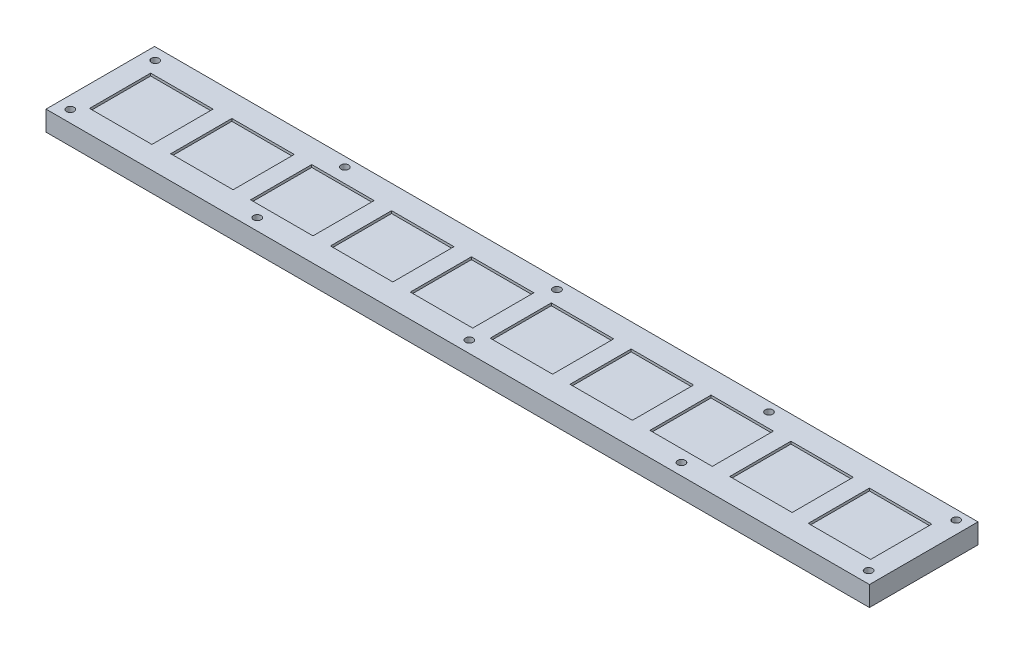
SolidWorks part; units mm, degrees
ref_plane "Front Plane" through (0, 0, 0) normal (0, 0, 1) x (1, 0, 0)
ref_plane "Top Plane" through (0, 0, 0) normal (0, 1, 0) x (1, 0, 0)
ref_plane "Right Plane" through (0, 0, 0) normal (1, 0, 0) x (0, 0, -1)
sketch "Sketch1" plane through (0, 0, 0) normal (0, 1, 0) x (1, 0, 0)
  line L1 (0, 0) -> (-330, 0)
  line L2 (0, 0) -> (0, 43.5)
  line L3 (0, 43.5) -> (-330, 43.5)
  line L4 (-330, 0) -> (-330, 43.5)
  dimension "D1" = 330
  dimension "D2" = 43.5
extrude "Boss-Extrude1" add sketch "Sketch1" along normal blind 8
sketch "Sketch6" plane through (0, 8, 0) normal (0, 1, 0) x (1, 0, 0)
  line L0 (-330, 21.75) -> (0, 21.75) construction
  line L1 (-330, 43.5) -> (-330, 0) construction
  line L2 (0, 0) -> (0, 43.5) construction
  line L3 (0, 21.75) -> (-165, 21.75) construction
  line L4 (-165, 21.75) -> (-165, 91.0768) construction
  line L5 (-165, 91.0768) -> (-165, -46.8957) construction
  line L6 (-225.5094, 9.5) -> (-225.5094, 34)
  line L7 (-193.5047, 9.5) -> (-168.5, 9.5)
  line L8 (-193.5047, 9.5) -> (-193.5047, 34)
  line L9 (-193.5047, 34) -> (-168.5, 34)
  line L10 (-168.5, 9.5) -> (-168.5, 34)
  line L11 (-193.5047, 9.5) -> (-168.5, 34) construction
  line L12 (-193.5047, 34) -> (-168.5, 9.5) construction
  line L13 (-225.5094, 34) -> (-200.5047, 34)
  line L14 (-200.5047, 9.5) -> (-200.5047, 34)
  line L15 (-225.5094, 9.5) -> (-200.5047, 9.5)
  line L16 (-257.5142, 9.5) -> (-257.5142, 34)
  line L17 (-257.5142, 34) -> (-232.5094, 34)
  line L18 (-232.5094, 9.5) -> (-232.5094, 34)
  line L19 (-257.5142, 9.5) -> (-232.5094, 9.5)
  line L20 (-289.5189, 9.5) -> (-289.5189, 34)
  line L21 (-289.5189, 34) -> (-264.5142, 34)
  line L22 (-264.5142, 9.5) -> (-264.5142, 34)
  line L23 (-289.5189, 9.5) -> (-264.5142, 9.5)
  line L24 (-321.5236, 8.9598) -> (-321.5236, 33.4598)
  line L25 (-321.5236, 33.4598) -> (-296.5189, 33.4598)
  line L26 (-296.5189, 8.9598) -> (-296.5189, 33.4598)
  line L27 (-321.5236, 8.9598) -> (-296.5189, 8.9598)
  line L28 (-136.4953, 9.5) -> (-136.4953, 34)
  line L29 (-136.4953, 9.5) -> (-161.5, 9.5)
  line L30 (-161.5, 9.5) -> (-161.5, 34)
  line L31 (-136.4953, 34) -> (-161.5, 34)
  line L32 (-104.4906, 9.5) -> (-104.4906, 34)
  line L33 (-104.4906, 9.5) -> (-129.4953, 9.5)
  line L34 (-129.4953, 9.5) -> (-129.4953, 34)
  line L35 (-104.4906, 34) -> (-129.4953, 34)
  line L36 (-72.4858, 9.5) -> (-72.4858, 34)
  line L37 (-72.4858, 9.5) -> (-97.4906, 9.5)
  line L38 (-97.4906, 9.5) -> (-97.4906, 34)
  line L39 (-72.4858, 34) -> (-97.4906, 34)
  line L40 (-40.4811, 9.5) -> (-40.4811, 34)
  line L41 (-40.4811, 9.5) -> (-65.4858, 9.5)
  line L42 (-65.4858, 9.5) -> (-65.4858, 34)
  line L43 (-40.4811, 34) -> (-65.4858, 34)
  line L44 (-8.4764, 8.9598) -> (-8.4764, 33.4598)
  line L45 (-8.4764, 33.4598) -> (-33.4811, 33.4598)
  line L46 (-33.4811, 8.9598) -> (-33.4811, 33.4598)
  line L47 (-8.4764, 8.9598) -> (-33.4811, 8.9598)
  line L48 (0, 43.5) -> (-330, 43.5) construction
  line L49 (-330, 0) -> (0, 0) construction
  point P6 (-181.0024, 21.75)
  dimension "D1" = 3.5
  dimension "D2" = 25.0047
  dimension "D3" = 24.5
  dimension "D8" = 7
  dimension "D9" = 7
  dimension "D10" = 7
  dimension "D11" = 7
  dimension "D12" = 9.5
  dimension "D13" = 9.5
  dimension "D4" = 2
  dimension "D5" = 2
  dimension "D6" = 2
  dimension "D7" = 2
extrude "Cut-Extrude1" cut sketch "Sketch6" against normal blind 1
hole_wizard "Tapped Hole for #4-40 Helicoil2" positions "Sketch14" profile "Sketch13" tap size "#4-40" standard "Helicoil® Inch" end condition through all
sketch "Sketch14" plane through (0, 8, 0) normal (0, 1, 0) x (1, 0, 0)
  line L1 (-330, 0) -> (0, 0) construction
  line L2 (-330, 43.5) -> (-330, 0) construction
  point P0 (-165, 39.7453)
  point P2 (-165, 4.664)
  point P4 (-250, 4.664)
  point P6 (-325, 4.75)
  point P8 (-325, 38.75)
  point P10 (-250, 39.7453)
  point P12 (-80, 39.7453)
  point P14 (-80, 4.664)
  point P16 (-5, 4.664)
  point P18 (-5, 39.7453)
  dimension "D2" = 4.75
  dimension "D3" = 38.75
  dimension "D7" = 5
  dimension "D8" = 80
  dimension "D9" = 165
  dimension "D11" = 250
  dimension "D12" = 325
cosmetic thread "Hole Thread2" parameters "D1"=3.56, "D2"=3.7414
cosmetic thread "Hole Thread3" parameters "D1"=3.56, "D2"=3.7414
cosmetic thread "Hole Thread4" parameters "D1"=3.56, "D2"=3.7414
cosmetic thread "Hole Thread5" parameters "D1"=3.56, "D2"=3.7414
cosmetic thread "Hole Thread6" parameters "D1"=3.56, "D2"=3.7414
cosmetic thread "Hole Thread7" parameters "D1"=3.56, "D2"=3.7414
cosmetic thread "Hole Thread8" parameters "D1"=3.56, "D2"=3.7414
cosmetic thread "Hole Thread9" parameters "D1"=3.56, "D2"=3.7414
cosmetic thread "Hole Thread10" parameters "D1"=3.56, "D2"=3.7414
cosmetic thread "Hole Thread11" parameters "D1"=3.56, "D2"=3.7414
sketch "Sketch13" plane through (-165, 8, -39.7453) normal (1, 0, 0) x (0, 0, 1)
  line L0 (0, 0) -> (0, 8)
  line L1 (0, 8) -> (1.524, 8)
  line L2 (1.524, 8) -> (1.524, 0)
  line L5 (1.524, 0) -> (0, 0)
  line L11 (0, -6.35) -> (0, 107.95) construction
  dimension "Thru Tap Drill Dia." = 3.048
  dimension "Thru Tap Drill Depth" = 8
